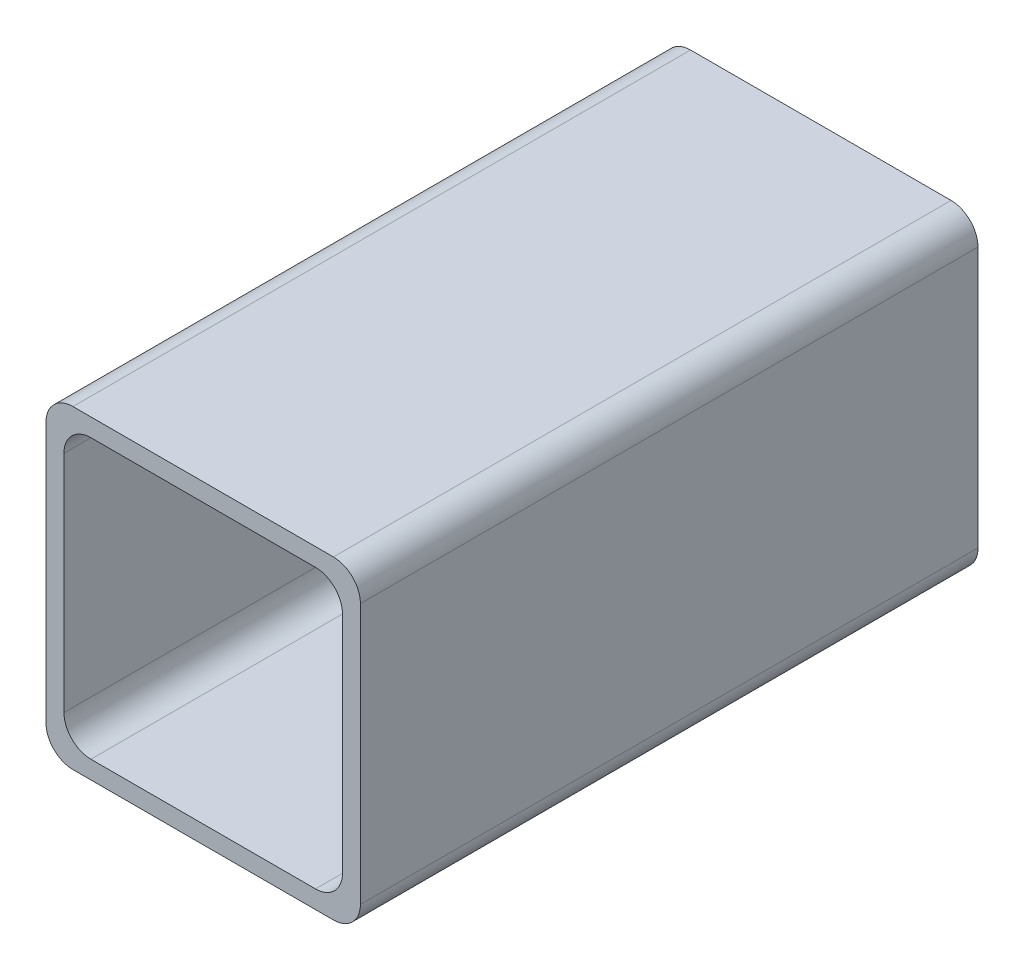
SolidWorks part; units mm, degrees
material "AISI 1020"
ref_plane "Спереди" through (0, 0, 0) normal (0, 0, 1) x (1, 0, 0)
ref_plane "Сверху" through (0, 0, 0) normal (0, 1, 0) x (1, 0, 0)
ref_plane "Справа" through (0, 0, 0) normal (1, 0, 0) x (0, 0, -1)
sketch "Эскиз1" plane through (0, 0, 0) normal (0, 0, 1) x (1, 0, 0)
  line L0 (-199.8423, 0) -> (9792.2745, 0) construction
  line L9 (0, -199.8423) -> (0, 9792.2745) construction
  line L10 (-15.5, -12.5) -> (-15.5, 12.5)
  line L11 (-12.5, 15.5) -> (12.5, 15.5)
  line L12 (14.5, 17.5) -> (-14.5, 17.5)
  line L13 (-17.5, 14.5) -> (-17.5, -14.5)
  line L14 (14.5, -17.5) -> (-14.5, -17.5)
  line L15 (-12.5, -15.5) -> (12.5, -15.5)
  line L16 (17.5, 14.5) -> (17.5, -14.5)
  line L17 (15.5, -12.5) -> (15.5, 12.5)
  arc A0 (-14.5, 17.5) -> (-17.5, 14.5) centre (-14.5, 14.5) ccw
  arc A1 (-15.5, 12.5) -> (-12.5, 15.5) centre (-12.5, 12.5) cw
  arc A2 (-15.5, -12.5) -> (-12.5, -15.5) centre (-12.5, -12.5) ccw
  arc A3 (-14.5, -17.5) -> (-17.5, -14.5) centre (-14.5, -14.5) cw
  arc A4 (14.5, -17.5) -> (17.5, -14.5) centre (14.5, -14.5) ccw
  arc A5 (15.5, -12.5) -> (12.5, -15.5) centre (12.5, -12.5) cw
  arc A6 (15.5, 12.5) -> (12.5, 15.5) centre (12.5, 12.5) ccw
  arc A7 (14.5, 17.5) -> (17.5, 14.5) centre (14.5, 14.5) cw
  point P20 (-15.5, 0)
  point P21 (-17.5, 0)
  point P24 (0, -17.5)
  point P25 (0, -15.5)
  point P26 (0, 15.5)
  point P27 (0, 17.5)
  point P35 (17.5, 0)
  point P36 (15.5, 0)
  dimension "_Rc" = 3
  dimension "D1" = 3
  dimension "_S" = 2
  dimension "_A" = 35
extrude "Бобышка-Вытянуть1" add sketch "Эскиз1" along normal offset from surface (68.75 mm away) 10
equation "\"D1@Эскиз1\"=\"_Rc@Эскиз1\""
